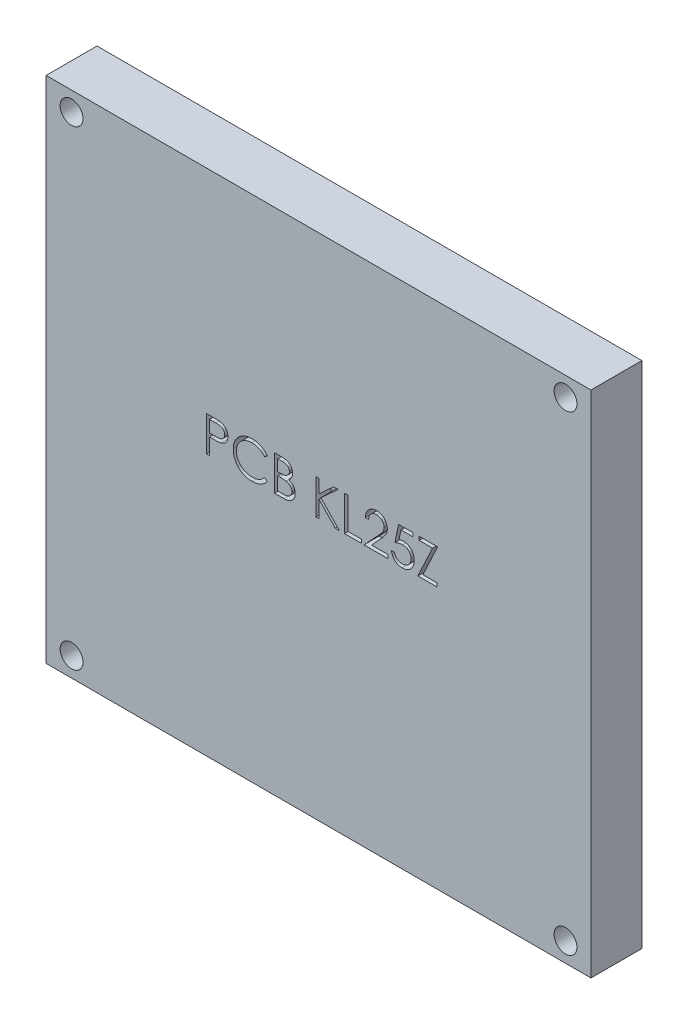
SolidWorks part; units mm, degrees
ref_plane "Alzado" through (0, 0, 0) normal (0, 0, 1) x (1, 0, 0)
ref_plane "Planta" through (0, 0, 0) normal (0, 1, 0) x (1, 0, 0)
ref_plane "Vista lateral" through (0, 0, 0) normal (1, 0, 0) x (0, 0, -1)
sketch "Croquis1" plane through (0, 0, 0) normal (0, 0, 1) x (1, 0, 0)
  line L1 (-44.2114, 42.431) -> (62.7886, 42.431)
  line L2 (-44.2114, 42.431) -> (-44.2114, -57.569)
  line L3 (-44.2114, -57.569) -> (62.7886, -57.569)
  line L4 (62.7886, 42.431) -> (62.7886, -57.569)
  dimension "D1" = 107
  dimension "D2" = 100
extrude "Saliente-Extruir1" add sketch "Croquis1" along normal blind 10
sketch "Croquis2" plane through (0, 0, 10) normal (0, 0, 1) x (1, 0, 0)
  text T0 "PCB KL25Z\r\n" font "Century Gothic" height in points 26
extrude "Cortar-Extruir1" cut sketch "Croquis2" against normal blind 3
sketch "Croquis4" plane through (0, 0, 10) normal (0, 0, 1) x (1, 0, 0)
  line L2 (62.7886, 42.431) -> (-44.2114, 42.431) construction
  line L3 (9.2886, 42.431) -> (9.2886, -57.569) construction
  line L4 (-44.2114, -57.569) -> (62.7886, -57.569) construction
  line L5 (62.7886, -57.569) -> (62.7886, 42.431) construction
  circle A0 centre (57.7886, 38.681) radius 2.25
  circle A1 centre (57.7886, -53.739) radius 2.25
  circle A2 centre (-39.2114, -53.739) radius 2.25
  circle A3 centre (-39.2114, 38.681) radius 2.25
  dimension "D1" = 4.5
  dimension "D4" = 4.5
  dimension "D5" = 5
  dimension "D2" = 5
  dimension "D3" = 3.75
  dimension "D6" = 3.83
extrude "Cortar-Extruir2" cut sketch "Croquis4" against normal blind 10
